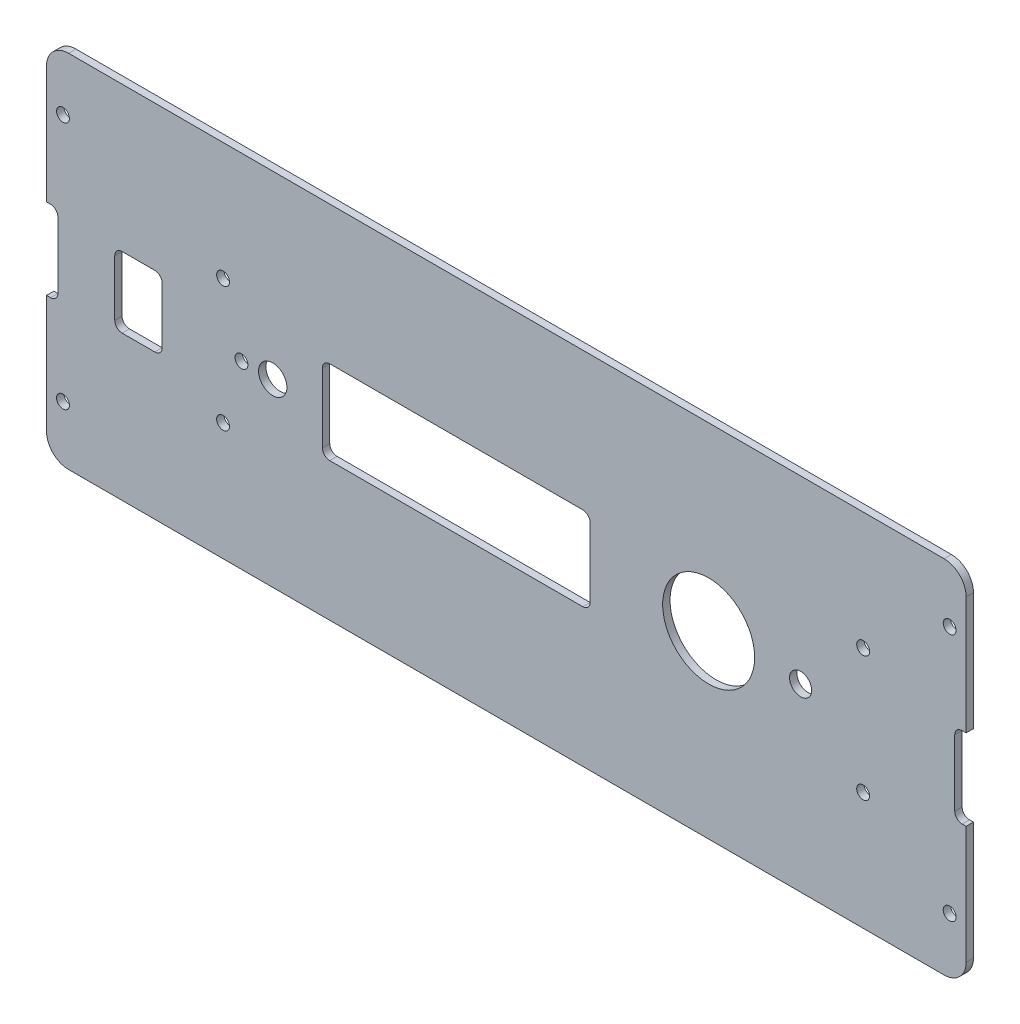
SolidWorks part; units mm, degrees
ref_plane "정면" through (0, 0, 0) normal (0, 0, 1) x (1, 0, 0)
ref_plane "윗면" through (0, 0, 0) normal (0, 1, 0) x (1, 0, 0)
ref_plane "우측면" through (0, 0, 0) normal (1, 0, 0) x (0, 0, -1)
sketch "Sketch1" plane through (0, 0, 0) normal (0, 0, 1) x (1, 0, 0)
  line L1 (-125, -49) -> (125, -49)
  line L2 (-125, -49) -> (-125, 49)
  line L3 (-125, 49) -> (125, 49)
  line L4 (125, -49) -> (125, 49)
  line L5 (-125, -49) -> (125, 49) construction
  line L6 (-125, 49) -> (125, -49) construction
  point P0 (0, 0)
  dimension "D1" = 250
  dimension "D2" = 98
extrude "Boss-Extrude1" add sketch "Sketch1" along normal blind 2 contours L3 L4 L1 L2
fillet "Fillet1" radius 6 4 edges at (-125, -49, 1) (125, -49, 1) (125, 49, 1) (-125, 49, 1)
sketch "Sketch2" plane through (0, 0, 2) normal (0, 0, 1) x (1, 0, 0)
  line L0 (0, 57.6898) -> (0, -71.1502) construction
  line L1 (-159.5207, 0) -> (171.5915, 0) construction
  line L2 (-125, -43) -> (-125, 43) construction
  line L3 (-128.1, -11) -> (-121.9, -11)
  line L4 (-128.1, -11) -> (-128.1, 11)
  line L5 (-128.1, 11) -> (-121.9, 11)
  line L6 (-121.9, -11) -> (-121.9, 11)
  line L7 (-128.1, -11) -> (-121.9, 11) construction
  line L8 (-128.1, 11) -> (-121.9, -11) construction
  line L9 (128.1, 11) -> (121.9, 11)
  line L10 (121.9, -11) -> (121.9, 11)
  line L11 (128.1, -11) -> (121.9, -11)
  line L12 (128.1, -11) -> (128.1, 11)
  line L13 (128.1, 11) -> (121.9, -11) construction
  line L14 (128.1, -11) -> (121.9, 11) construction
  point P5 (-125, 0)
  point P16 (125, 0)
  dimension "D1" = 22
  dimension "D2" = 3.1
extrude "Cut-Extrude1" cut sketch "Sketch2" against normal blind 12
fillet "Fillet2" radius 2 4 edges at (121.9, -11, 1) (121.9, 11, 1) (-121.9, -11, 1) (-121.9, 11, 1)
hole_wizard "Ø3.5 (3.5) Diameter Hole1" positions "Sketch4" profile "Sketch3" hole size "Ø3.5" standard "ANSI Metric" end condition through all
sketch "Sketch4" plane through (0, 0, 2) normal (0, 0, 1) x (1, 0, 0)
  line L0 (-125, 11) -> (-125, 43) construction
  line L1 (125, 11) -> (125, 43) construction
  line L2 (-139.1401, 0) -> (160.4598, 0) construction
  point P0 (-120.52, 33.75)
  point P2 (-120.52, -33.75)
  point P4 (120.52, -33.75)
  point P6 (120.52, 33.75)
  dimension "D1" = 67.5
  dimension "D2" = 4.48
  dimension "D3" = 4.48
  dimension "D4" = 33.75
sketch "Sketch3" plane through (-120.52, 33.75, 2) normal (1, 0, 0) x (0, -1, 0)
  line L0 (0, 0) -> (0, 2)
  line L1 (0, 2) -> (1.75, 2)
  line L2 (1.75, 2) -> (1.75, 0)
  line L5 (1.75, 0) -> (0, 0)
  line L11 (0, -6.35) -> (0, 107.95) construction
  dimension "Thru Hole Dia." = 3.5
  dimension "Thru Hole Depth" = 2
sketch "Sketch5" plane through (0, 0, 2) normal (0, 0, 1) x (1, 0, 0)
  line L0 (-142.3063, 0) -> (137.5035, 0) construction
  line L1 (-80, -20) -> (100, -20)
  line L2 (-80, -20) -> (-80, 20)
  line L3 (-80, 20) -> (100, 20)
  line L4 (100, -20) -> (100, 20)
  line L5 (-80, -20) -> (100, 20) construction
  line L6 (-80, 20) -> (100, -20) construction
  line L7 (10, 76.9671) -> (10, -55.0884) construction
  line L8 (-125, 11) -> (-125, 43) construction
  point P0 (10, 0)
  dimension "D3" = 135
  dimension "D1" = 180
  dimension "D2" = 40
sketch "Sketch6" plane through (0, 0, 2) normal (0, 0, 1) x (1, 0, 0)
  line L0 (-80, -20) -> (-80, 20) construction
  line L1 (-80, 20) -> (100, 20) construction
  line L2 (100, -20) -> (100, 20) construction
  line L3 (-80, -20) -> (100, -20) construction
  line L4 (-142.3063, 0) -> (137.5035, 0) construction
  line L6 (-50, -11.4) -> (22.8, -11.4)
  line L7 (-50, -11.4) -> (-50, 11.4)
  line L8 (-50, 11.4) -> (22.8, 11.4)
  line L9 (22.8, -11.4) -> (22.8, 11.4)
  line L10 (-50, -11.4) -> (22.8, 11.4) construction
  line L11 (-50, 11.4) -> (22.8, -11.4) construction
  line L12 (-106.45, -9.6) -> (-93.55, -9.6)
  line L13 (-106.45, -9.6) -> (-106.45, 9.6)
  line L14 (-106.45, 9.6) -> (-93.55, 9.6)
  line L15 (-93.55, -9.6) -> (-93.55, 9.6)
  line L16 (-106.45, -9.6) -> (-93.55, 9.6) construction
  line L17 (-106.45, 9.6) -> (-93.55, -9.6) construction
  circle A0 centre (-77, 17) radius 1.75
  circle A1 centre (-77, -17) radius 1.75
  circle A2 centre (97, 17) radius 1.75
  circle A3 centre (97, -17) radius 1.75
  circle A4 centre (-72, 0) radius 1.75
  circle A5 centre (-63.5, 0) radius 3.855
  circle A6 centre (55, 0) radius 12.5
  circle A7 centre (80, 0) radius 3
  point P22 (-13.6, 0)
  point P31 (-100, 0)
  dimension "D1" = 3.5
  dimension "D6" = 3.5
  dimension "D8" = 16.5
  dimension "D9" = 7.71
  dimension "D13" = 25
  dimension "D15" = 6
  dimension "D2" = 3
  dimension "D3" = 3
  dimension "D4" = 3
  dimension "D5" = 3
  dimension "D7" = 8
  dimension "D10" = 30
  dimension "D11" = 72.8
  dimension "D12" = 22.8
  dimension "D14" = 135
  dimension "D16" = 160
  dimension "D17" = 12.9
  dimension "D18" = 19.2
  dimension "D19" = 20
extrude "Cut-Extrude2" cut sketch "Sketch6" against normal blind 12
fillet "Fillet3" radius 2 8 edges at (-50, -11.4, 1) (22.8, -11.4, 1) (22.8, 11.4, 1) (-50, 11.4, 1) (-106.45, -9.6, 1) (-93.55, -9.6, 1) (-93.55, 9.6, 1) (-106.45, 9.6, 1)
